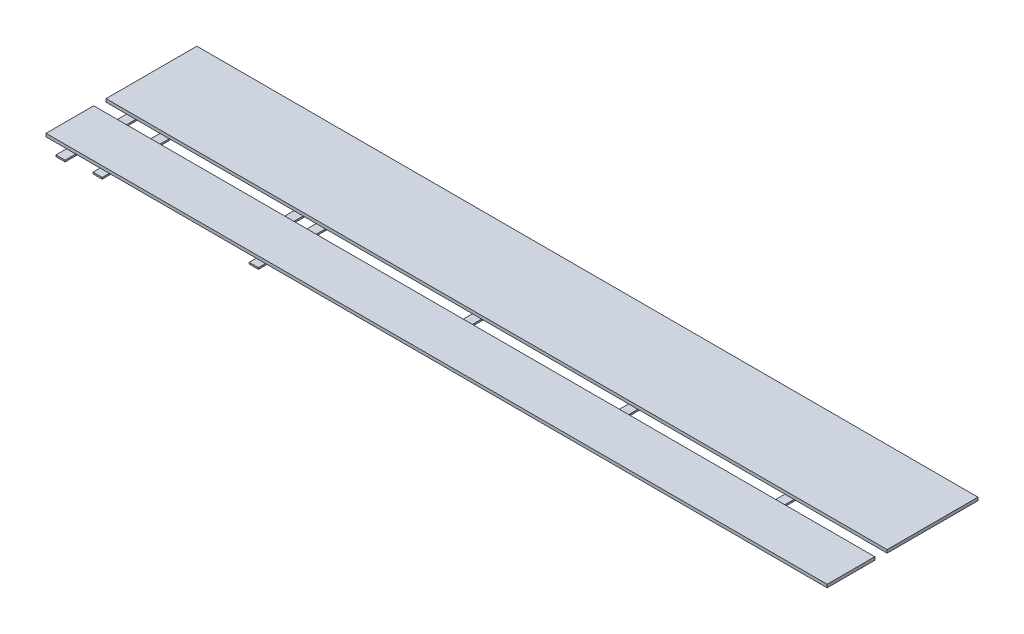
SolidWorks part; units mm, degrees
ref_plane "Front Plane" through (0, 0, 0) normal (0, 0, 1) x (1, 0, 0)
ref_plane "Top Plane" through (0, 0, 0) normal (0, 1, 0) x (1, 0, 0)
ref_plane "Right Plane" through (0, 0, 0) normal (1, 0, 0) x (0, 0, -1)
sketch "Sketch2" plane through (0, 0, 0) normal (0, 1, 0) x (1, 0, 0)
  line L0 (23, 0) -> (23, 355.0006)
  line L1 (23, 355.0006) -> (42.05, 355.0006)
  line L2 (42.05, 355.0006) -> (42.05, 0)
  line L3 (42.05, 0) -> (23, 0)
  line L4 (42.05, 177.5003) -> (23, 177.5003)
  line L5 (32.525, 177.5003) -> (32.525, 167.5003)
  line L6 (32.525, 177.5003) -> (32.525, 187.5003)
  line L7 (55.525, 177.5003) -> (55.525, 167.5003)
  line L8 (55.525, 177.5003) -> (55.525, 187.5003)
  line L9 (78.525, 177.5003) -> (78.525, 167.5003)
  line L10 (78.525, 177.5003) -> (78.525, 187.5003)
  line L11 (101.525, 177.5003) -> (101.525, 167.5003)
  line L12 (101.525, 177.5003) -> (101.525, 187.5003)
  line L13 (124.525, 177.5003) -> (124.525, 167.5003)
  line L14 (124.525, 177.5003) -> (124.525, 187.5003)
  line L15 (147.525, 177.5003) -> (147.525, 167.5003)
  line L16 (147.525, 177.5003) -> (147.525, 187.5003)
  line L17 (170.525, 177.5003) -> (170.525, 167.5003)
  line L18 (170.525, 177.5003) -> (170.525, 187.5003)
  line L19 (193.525, 177.5003) -> (193.525, 167.5003)
  line L20 (193.525, 177.5003) -> (193.525, 187.5003)
  line L21 (216.525, 177.5003) -> (216.525, 167.5003)
  line L22 (216.525, 177.5003) -> (216.525, 187.5003)
  line L23 (239.525, 177.5003) -> (239.525, 167.5003)
  line L24 (239.525, 177.5003) -> (239.525, 187.5003)
  line L25 (262.525, 177.5003) -> (262.525, 167.5003)
  line L26 (262.525, 177.5003) -> (262.525, 187.5003)
  line L27 (285.525, 177.5003) -> (285.525, 167.5003)
  line L28 (285.525, 177.5003) -> (285.525, 187.5003)
  line L29 (308.525, 177.5003) -> (308.525, 167.5003)
  line L30 (308.525, 177.5003) -> (308.525, 187.5003)
  line L31 (331.525, 177.5003) -> (331.525, 167.5003)
  line L32 (331.525, 177.5003) -> (331.525, 187.5003)
  line L33 (354.525, 177.5003) -> (354.525, 167.5003)
  line L34 (354.525, 177.5003) -> (354.525, 187.5003)
  line L35 (377.525, 177.5003) -> (377.525, 167.5003)
  line L36 (377.525, 177.5003) -> (377.525, 187.5003)
  line L37 (400.525, 177.5003) -> (400.525, 167.5003)
  line L38 (400.525, 177.5003) -> (400.525, 187.5003)
  line L39 (423.525, 177.5003) -> (423.525, 167.5003)
  line L40 (423.525, 177.5003) -> (423.525, 187.5003)
  line L41 (446.525, 177.5003) -> (446.525, 167.5003)
  line L42 (446.525, 177.5003) -> (446.525, 187.5003)
  line L43 (469.525, 177.5003) -> (469.525, 167.5003)
  line L44 (469.525, 177.5003) -> (469.525, 187.5003)
  line L45 (492.525, 177.5003) -> (492.525, 167.5003)
  line L46 (492.525, 177.5003) -> (492.525, 187.5003)
  line L47 (515.525, 177.5003) -> (515.525, 167.5003)
  line L48 (515.525, 177.5003) -> (515.525, 187.5003)
  line L49 (538.525, 177.5003) -> (538.525, 167.5003)
  line L50 (538.525, 177.5003) -> (538.525, 187.5003)
  line L51 (561.525, 177.5003) -> (561.525, 167.5003)
  line L52 (561.525, 177.5003) -> (561.525, 187.5003)
  line L53 (584.525, 177.5003) -> (584.525, 167.5003)
  line L54 (584.525, 177.5003) -> (584.525, 187.5003)
  line L55 (607.525, 177.5003) -> (607.525, 167.5003)
  line L56 (607.525, 177.5003) -> (607.525, 187.5003)
  line L57 (630.525, 177.5003) -> (630.525, 167.5003)
  line L58 (630.525, 177.5003) -> (630.525, 187.5003)
  line L59 (653.525, 177.5003) -> (653.525, 167.5003)
  line L60 (653.525, 177.5003) -> (653.525, 187.5003)
  line L61 (676.525, 177.5003) -> (676.525, 167.5003)
  line L62 (676.525, 177.5003) -> (676.525, 187.5003)
  line L63 (699.525, 177.5003) -> (699.525, 167.5003)
  line L64 (699.525, 177.5003) -> (699.525, 187.5003)
  line L65 (722.525, 177.5003) -> (722.525, 167.5003)
  line L66 (722.525, 177.5003) -> (722.525, 187.5003)
  line L67 (745.525, 177.5003) -> (745.525, 167.5003)
  line L68 (745.525, 177.5003) -> (745.525, 187.5003)
  line L69 (768.525, 177.5003) -> (768.525, 167.5003)
  line L70 (768.525, 177.5003) -> (768.525, 187.5003)
  line L71 (791.525, 177.5003) -> (791.525, 167.5003)
  line L72 (791.525, 177.5003) -> (791.525, 187.5003)
  line L73 (814.525, 177.5003) -> (814.525, 167.5003)
  line L74 (814.525, 177.5003) -> (814.525, 187.5003)
  line L75 (837.525, 177.5003) -> (837.525, 167.5003)
  line L76 (837.525, 177.5003) -> (837.525, 187.5003)
  line L77 (860.525, 177.5003) -> (860.525, 167.5003)
  line L78 (860.525, 177.5003) -> (860.525, 187.5003)
  line L79 (883.525, 177.5003) -> (883.525, 167.5003)
  line L80 (883.525, 177.5003) -> (883.525, 187.5003)
  line L81 (906.525, 177.5003) -> (906.525, 167.5003)
  line L82 (906.525, 177.5003) -> (906.525, 187.5003)
  line L83 (929.525, 177.5003) -> (929.525, 167.5003)
  line L84 (929.525, 177.5003) -> (929.525, 187.5003)
  line L85 (952.525, 177.5003) -> (952.525, 167.5003)
  line L86 (952.525, 177.5003) -> (952.525, 187.5003)
  line L87 (975.525, 177.5003) -> (975.525, 167.5003)
  line L88 (975.525, 177.5003) -> (975.525, 187.5003)
  line L89 (998.525, 177.5003) -> (998.525, 167.5003)
  line L90 (998.525, 177.5003) -> (998.525, 187.5003)
  line L91 (1021.525, 177.5003) -> (1021.525, 167.5003)
  line L92 (1021.525, 177.5003) -> (1021.525, 187.5003)
  line L93 (1044.525, 177.5003) -> (1044.525, 167.5003)
  line L94 (1044.525, 177.5003) -> (1044.525, 187.5003)
  line L95 (1067.525, 177.5003) -> (1067.525, 167.5003)
  line L96 (1067.525, 177.5003) -> (1067.525, 187.5003)
  line L97 (1090.525, 177.5003) -> (1090.525, 167.5003)
  line L98 (1090.525, 177.5003) -> (1090.525, 187.5003)
  line L99 (1113.525, 177.5003) -> (1113.525, 167.5003)
  line L100 (1113.525, 177.5003) -> (1113.525, 187.5003)
  line L101 (1136.525, 177.5003) -> (1136.525, 167.5003)
  line L102 (1136.525, 177.5003) -> (1136.525, 187.5003)
  line L103 (-3.95, 177.5003) -> (-23, 177.5003)
  line L104 (-13.475, 177.5003) -> (-13.475, 187.5003)
  line L105 (65.05, 177.5003) -> (46, 177.5003)
  line L106 (88.05, 177.5003) -> (69, 177.5003)
  line L107 (111.05, 177.5003) -> (92, 177.5003)
  line L108 (134.05, 177.5003) -> (115, 177.5003)
  line L109 (157.05, 177.5003) -> (138, 177.5003)
  line L110 (180.05, 177.5003) -> (161, 177.5003)
  line L111 (203.05, 177.5003) -> (184, 177.5003)
  line L112 (226.05, 177.5003) -> (207, 177.5003)
  line L113 (249.05, 177.5003) -> (230, 177.5003)
  line L114 (272.05, 177.5003) -> (253, 177.5003)
  line L115 (295.05, 177.5003) -> (276, 177.5003)
  line L116 (318.05, 177.5003) -> (299, 177.5003)
  line L117 (341.05, 177.5003) -> (322, 177.5003)
  line L118 (364.05, 177.5003) -> (345, 177.5003)
  line L119 (387.05, 177.5003) -> (368, 177.5003)
  line L120 (410.05, 177.5003) -> (391, 177.5003)
  line L121 (433.05, 177.5003) -> (414, 177.5003)
  line L122 (456.05, 177.5003) -> (437, 177.5003)
  line L123 (479.05, 177.5003) -> (460, 177.5003)
  line L124 (502.05, 177.5003) -> (483, 177.5003)
  line L125 (525.05, 177.5003) -> (506, 177.5003)
  line L126 (548.05, 177.5003) -> (529, 177.5003)
  line L127 (571.05, 177.5003) -> (552, 177.5003)
  line L128 (594.05, 177.5003) -> (575, 177.5003)
  line L129 (617.05, 177.5003) -> (598, 177.5003)
  line L130 (640.05, 177.5003) -> (621, 177.5003)
  line L131 (663.05, 177.5003) -> (644, 177.5003)
  line L132 (686.05, 177.5003) -> (667, 177.5003)
  line L133 (709.05, 177.5003) -> (690, 177.5003)
  line L134 (732.05, 177.5003) -> (713, 177.5003)
  line L135 (755.05, 177.5003) -> (736, 177.5003)
  line L136 (778.05, 177.5003) -> (759, 177.5003)
  line L137 (801.05, 177.5003) -> (782, 177.5003)
  line L138 (824.05, 177.5003) -> (805, 177.5003)
  line L139 (847.05, 177.5003) -> (828, 177.5003)
  line L140 (870.05, 177.5003) -> (851, 177.5003)
  line L141 (893.05, 177.5003) -> (874, 177.5003)
  line L142 (916.05, 177.5003) -> (897, 177.5003)
  line L143 (939.05, 177.5003) -> (920, 177.5003)
  line L144 (962.05, 177.5003) -> (943, 177.5003)
  line L145 (985.05, 177.5003) -> (966, 177.5003)
  line L146 (1008.05, 177.5003) -> (989, 177.5003)
  line L147 (1031.05, 177.5003) -> (1012, 177.5003)
  line L148 (1054.05, 177.5003) -> (1035, 177.5003)
  line L149 (1077.05, 177.5003) -> (1058, 177.5003)
  line L150 (1100.05, 177.5003) -> (1081, 177.5003)
  line L151 (1123.05, 177.5003) -> (1104, 177.5003)
  line L152 (1146.05, 177.5003) -> (1127, 177.5003)
  line L153 (-13.475, 177.5003) -> (-13.475, 167.5003)
  line L154 (345, 177.5003) -> (345, 303.0106)
  line L155 (345, 303.0106) -> (364.05, 303.0106)
  line L156 (364.05, 303.0106) -> (364.05, 51.99)
  line L157 (364.05, 51.99) -> (345, 51.99)
  line L158 (345, 51.99) -> (345, 177.5003)
  line L159 (667, 177.5003) -> (667, 266.2276)
  line L160 (667, 266.2276) -> (686.05, 266.2276)
  line L161 (686.05, 266.2276) -> (686.05, 88.773)
  line L162 (686.05, 88.773) -> (667, 88.773)
  line L163 (667, 88.773) -> (667, 177.5003)
  line L164 (989, 177.5003) -> (989, 240.2243)
  line L165 (989, 240.2243) -> (1008.05, 240.2243)
  line L166 (1008.05, 240.2243) -> (1008.05, 114.7763)
  line L167 (1008.05, 114.7763) -> (989, 114.7763)
  line L168 (989, 114.7763) -> (989, 177.5003)
  line L169 (1311, 177.5003) -> (1311, 221.8207)
  line L170 (1311, 221.8207) -> (1330.05, 221.8207)
  line L171 (1330.05, 221.8207) -> (1330.05, 133.1798)
  line L172 (1330.05, 133.1798) -> (1311, 133.1798)
  line L173 (1311, 133.1798) -> (1311, 177.5003)
  line L174 (-26.95, 177.5003) -> (-46, 177.5003)
  line L175 (1159.525, 177.5003) -> (1159.525, 167.5003) [skipped]
  line L176 (1159.525, 177.5003) -> (1159.525, 187.5003) [skipped]
  line L177 (1169.05, 177.5003) -> (1150, 177.5003) [skipped]
  line L178 (-36.475, 177.5003) -> (-36.475, 187.5003)
  line L179 (-36.475, 177.5003) -> (-36.475, 167.5003)
  line L180 (-26.95, 177.5003) -> (-26.95, 365.5543)
  line L181 (-26.95, 365.5543) -> (-46, 365.5543)
  line L182 (-46, 365.5543) -> (-46, -10.5537)
  line L183 (-46, -10.5537) -> (-26.95, -10.5537)
  line L184 (-26.95, -10.5537) -> (-26.95, 177.5003)
  line L185 (-36.475, 177.5003) -> (-36.475, 74.0706)
  line L186 (32.525, 177.5003) -> (32.525, 79.8751)
  line L187 (308.525, 177.5003) -> (308.525, 108.4802)
  line L188 (584.525, 177.5003) -> (584.525, 128.7085)
  line L189 (860.525, 177.5003) -> (860.525, 143.0084)
  line L190 (1136.525, 177.5003) -> (1136.525, 153.1172)
  line L191 (1169.05, 177.5003) -> (1150, 177.5003)
  line L192 (1159.525, 177.5003) -> (1159.525, 187.5003)
  line L193 (1159.525, 177.5003) -> (1159.525, 167.5003)
  line L194 (1192.05, 177.5003) -> (1173, 177.5003)
  line L195 (1182.525, 177.5003) -> (1182.525, 187.5003)
  line L196 (1182.525, 177.5003) -> (1182.525, 167.5003)
  line L197 (1215.05, 177.5003) -> (1196, 177.5003)
  line L198 (1205.525, 177.5003) -> (1205.525, 187.5003)
  line L199 (1205.525, 177.5003) -> (1205.525, 167.5003)
  line L200 (1238.05, 177.5003) -> (1219, 177.5003)
  line L201 (1228.525, 177.5003) -> (1228.525, 187.5003)
  line L202 (1228.525, 177.5003) -> (1228.525, 167.5003)
  line L203 (1261.05, 177.5003) -> (1242, 177.5003)
  line L204 (1251.525, 177.5003) -> (1251.525, 187.5003)
  line L205 (1251.525, 177.5003) -> (1251.525, 167.5003)
  line L206 (1284.05, 177.5003) -> (1265, 177.5003)
  line L207 (1274.525, 177.5003) -> (1274.525, 187.5003)
  line L208 (1274.525, 177.5003) -> (1274.525, 167.5003)
  line L209 (1307.05, 177.5003) -> (1288, 177.5003)
  line L210 (1297.525, 177.5003) -> (1297.525, 187.5003)
  line L211 (1297.525, 177.5003) -> (1297.525, 167.5003)
  line L212 (1330.05, 177.5003) -> (1311, 177.5003)
  line L213 (1320.525, 177.5003) -> (1320.525, 187.5003)
  line L214 (1320.525, 177.5003) -> (1320.525, 167.5003)
  line L215 (32.525, 177.5003) -> (32.525, 51.99)
  line L216 (32.525, 51.99) -> (42.05, 51.99)
  line L217 (32.525, 51.99) -> (23, 51.99)
  line L218 (32.525, 177.5003) -> (32.525, 303.0106)
  line L219 (32.525, 303.0106) -> (42.05, 303.0106)
  line L220 (32.525, 303.0106) -> (23, 303.0106)
  line L221 (-36.475, 177.5003) -> (-36.475, 44.5059)
  line L222 (-36.475, 177.5003) -> (-36.475, 310.4947)
  line L223 (-46, 44.5059) -> (-26.95, 44.5059)
  line L224 (-46, 310.4947) -> (-26.95, 310.4947)
  line L225 (-36.475, 310.4947) -> (-36.475, 250.9132)
  line L226 (32.525, 303.0106) -> (32.525, 246.7974)
  line L227 (299, 177.5003) -> (299, 86.1238)
  line L228 (299, 86.1238) -> (318.05, 86.1238)
  line L229 (318.05, 86.1238) -> (318.05, 268.8768)
  line L230 (318.05, 268.8768) -> (299, 268.8768)
  line L231 (299, 268.8768) -> (299, 177.5003)
  line L232 (308.525, 268.8768) -> (308.525, 227.9398)
  circle A4 centre (354.525, 108.4802) radius 2
  circle A5 centre (354.525, 246.5203) radius 2
  circle A6 centre (676.525, 128.7085) radius 2
  circle A7 centre (676.525, 226.292) radius 2
  circle A8 centre (998.525, 143.0084) radius 2
  circle A9 centre (998.525, 211.9922) radius 2
  circle A10 centre (1320.525, 153.1172) radius 2
  circle A11 centre (1320.525, 201.8834) radius 2
  circle A12 centre (-36.475, 250.9132) radius 2
  circle A13 centre (-36.475, 104.0874) radius 2
  circle A14 centre (32.525, 246.7974) radius 2
  circle A15 centre (32.525, 108.2032) radius 2
  circle A16 centre (308.525, 227.9398) radius 2
  circle A17 centre (308.525, 127.0608) radius 2
  dimension "D5" = 9
  dimension "D1" = 50
  dimension "D3" = 2
  dimension "D2" = 50
  dimension "D4" = 2
extrude "Boss-Extrude1" add sketch "Sketch2" along normal blind 3.175
sketch "Sketch3" plane through (0, 3.175, 0) normal (0, 1, 0) x (1, 0, 0)
  line L0 (1330.05, 221.8207) -> (1330.05, 133.1798) construction
  line L1 (-46, 310.4947) -> (-46, 44.5059) construction
  line L2 (1330.05, 221.8207) -> (1330.05, 133.1798)
  line L3 (-46, 310.4947) -> (-46, 44.5059)
  line L4 (-46, 177.5003) -> (1330.05, 177.5003)
  line L5 (-46, 164.8003) -> (1330.05, 164.8003)
  line L6 (-46, 190.2003) -> (1330.05, 190.2003)
  line L7 (-46, 66.5003) -> (1330.05, 66.5003)
  line L8 (-46, 377.5003) -> (1330.05, 377.5003)
  line L9 (-26.95, 44.5059) -> (-26.95, 310.4947) construction
  line L10 (-26.95, 44.5059) -> (-26.95, 310.4947)
  line L11 (-46, 177.5003) -> (-26.95, 177.5003)
  line L12 (-36.475, 177.5003) -> (-88.375, 177.5003)
  line L13 (-46, 66.5003) -> (-88.375, 66.5003)
  line L14 (-88.375, 66.5003) -> (-88.375, 164.8003)
  line L15 (-88.375, 164.8003) -> (-46, 164.8003)
  line L16 (-46, 190.2003) -> (-88.375, 190.2003)
  line L17 (-88.375, 190.2003) -> (-88.375, 377.5003)
  line L18 (-88.375, 377.5003) -> (-46, 377.5003)
  line L19 (1311, 133.1798) -> (1311, 221.8207) construction
  line L20 (1311, 133.1798) -> (1311, 221.8207)
  line L21 (1330.05, 177.5003) -> (1311, 177.5003)
  line L22 (1320.525, 177.5003) -> (1521.795, 177.5003)
  line L23 (1330.05, 66.5003) -> (1521.795, 66.5003)
  line L24 (1521.795, 66.5003) -> (1521.795, 164.8003)
  line L25 (1521.795, 164.8003) -> (1330.05, 164.8003)
  line L26 (1330.05, 190.2003) -> (1521.795, 190.2003)
  line L27 (1521.795, 190.2003) -> (1521.795, 377.5003)
  line L28 (1521.795, 377.5003) -> (1330.05, 377.5003)
  dimension "D1" = 12.7
  dimension "D2" = 12.7
  dimension "D3" = 98.3
  dimension "D4" = 187.3
extrude "Boss-Extrude2" add sketch "Sketch3" along normal blind 6.35 separate body
